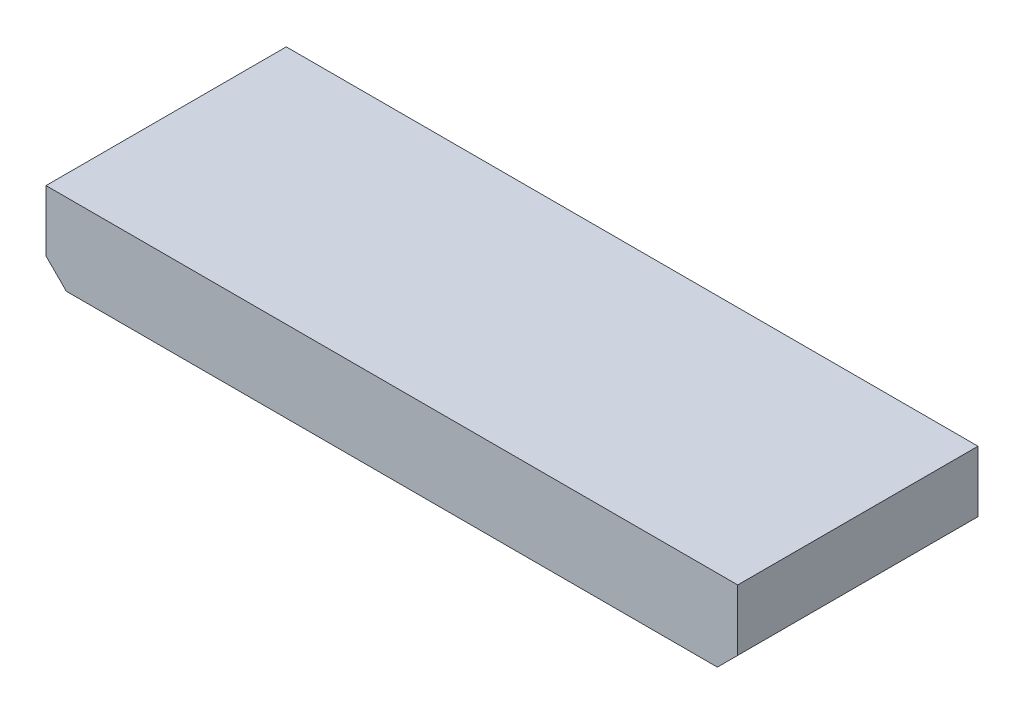
SolidWorks part; units mm, degrees
ref_plane "Front Plane" through (0, 0, 0) normal (0, 0, 1) x (1, 0, 0)
ref_plane "Top Plane" through (0, 0, 0) normal (0, 1, 0) x (1, 0, 0)
ref_plane "Right Plane" through (0, 0, 0) normal (1, 0, 0) x (0, 0, -1)
sketch "Sketch1" plane through (0, 0, 0) normal (0, 0, 1) x (1, 0, 0)
  line L0 (-5.08, 2.54) -> (-5.08, -1.27)
  line L1 (-5.08, -1.27) -> (-3.81, -2.54)
  line L2 (-3.81, -2.54) -> (36.83, -2.54)
  line L3 (36.83, -2.54) -> (38.1, -1.27)
  line L4 (38.1, -1.27) -> (38.1, 2.54)
  line L5 (38.1, 2.54) -> (-5.08, 2.54)
extrude "Component_Outline" add sketch "Sketch1" along normal blind 15 separate body
sketch "Sketch2" plane through (0, 0, 0) normal (0, 0, 1) x (1, 0, 0)
  circle A0 centre (0, 0) radius 0.25
extrude "1" add sketch "Sketch2" against normal blind 2 separate body
sketch "Sketch3" plane through (0, 0, 0) normal (0, 0, 1) x (1, 0, 0)
  circle A0 centre (2.54, 0) radius 0.25
extrude "2" add sketch "Sketch3" against normal blind 2 separate body
sketch "Sketch4" plane through (0, 0, 0) normal (0, 0, 1) x (1, 0, 0)
  circle A0 centre (5.08, 0) radius 0.25
extrude "3" add sketch "Sketch4" against normal blind 2 separate body
sketch "Sketch5" plane through (0, 0, 0) normal (0, 0, 1) x (1, 0, 0)
  circle A0 centre (7.62, 0) radius 0.25
extrude "4" add sketch "Sketch5" against normal blind 2 separate body
sketch "Sketch6" plane through (0, 0, 0) normal (0, 0, 1) x (1, 0, 0)
  circle A0 centre (10.16, 0) radius 0.25
extrude "5" add sketch "Sketch6" against normal blind 2 separate body
sketch "Sketch7" plane through (0, 0, 0) normal (0, 0, 1) x (1, 0, 0)
  circle A0 centre (12.7, 0) radius 0.25
extrude "6" add sketch "Sketch7" against normal blind 2 separate body
sketch "Sketch8" plane through (0, 0, 0) normal (0, 0, 1) x (1, 0, 0)
  circle A0 centre (15.24, 0) radius 0.25
extrude "7" add sketch "Sketch8" against normal blind 2 separate body
sketch "Sketch9" plane through (0, 0, 0) normal (0, 0, 1) x (1, 0, 0)
  circle A0 centre (17.78, 0) radius 0.25
extrude "8" add sketch "Sketch9" against normal blind 2 separate body
sketch "Sketch10" plane through (0, 0, 0) normal (0, 0, 1) x (1, 0, 0)
  circle A0 centre (20.32, 0) radius 0.25
extrude "9" add sketch "Sketch10" against normal blind 2 separate body
sketch "Sketch11" plane through (0, 0, 0) normal (0, 0, 1) x (1, 0, 0)
  circle A0 centre (22.86, 0) radius 0.25
extrude "10" add sketch "Sketch11" against normal blind 2 separate body
sketch "Sketch12" plane through (0, 0, 0) normal (0, 0, 1) x (1, 0, 0)
  circle A0 centre (25.4, 0) radius 0.25
extrude "11" add sketch "Sketch12" against normal blind 2 separate body
sketch "Sketch13" plane through (0, 0, 0) normal (0, 0, 1) x (1, 0, 0)
  circle A0 centre (27.94, 0) radius 0.25
extrude "12" add sketch "Sketch13" against normal blind 2 separate body
sketch "Sketch14" plane through (0, 0, 0) normal (0, 0, 1) x (1, 0, 0)
  circle A0 centre (30.48, 0) radius 0.25
extrude "13" add sketch "Sketch14" against normal blind 2 separate body
sketch "Sketch15" plane through (0, 0, 0) normal (0, 0, 1) x (1, 0, 0)
  circle A0 centre (33.02, 0) radius 0.25
extrude "14" add sketch "Sketch15" against normal blind 2 separate body
sketch3d "3DSketch1"
  line L0 (0, 0, 0) -> (1, 0, 0)
  line L1 (0, 0, 0) -> (0, 1, 0)
  line L2 (0, 0, 0) -> (0, 0, 1)
  point P0 (0, 0, 0)
